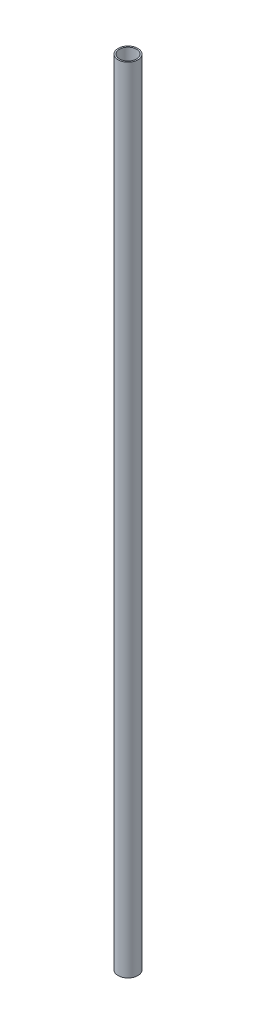
SolidWorks part; units mm, degrees
ref_plane "Front Plane" through (0, 0, 0) normal (0, 0, 1) x (1, 0, 0)
ref_plane "Top Plane" through (0, 0, 0) normal (0, 1, 0) x (1, 0, 0)
ref_plane "Right Plane" through (0, 0, 0) normal (1, 0, 0) x (0, 0, -1)
sketch "Sketch1" plane through (0, 0, 0) normal (0, 1, 0) x (1, 0, 0)
  circle A0 centre (0, 0) radius 6.35
  circle A1 centre (0, 0) radius 5.461
  dimension "D1" = 12.7
  dimension "D2" = 0.889
extrude "Boss-Extrude1" add sketch "Sketch1" along normal blind 508
